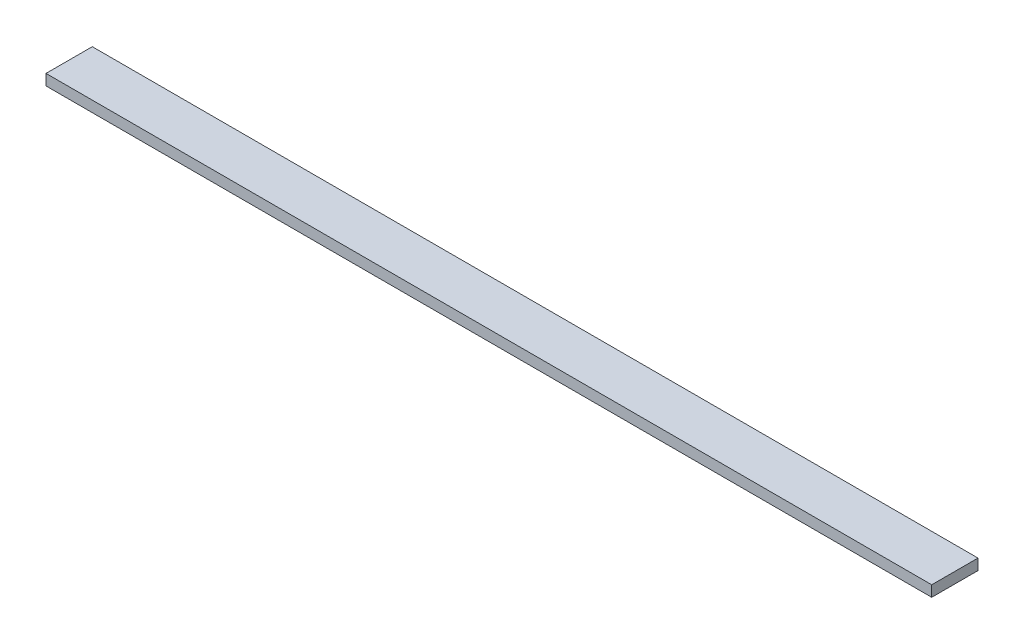
SolidWorks part; units mm, degrees
ref_plane "Front Plane" through (0, 0, 0) normal (0, 0, 1) x (1, 0, 0)
ref_plane "Top Plane" through (0, 0, 0) normal (0, 1, 0) x (1, 0, 0)
ref_plane "Right Plane" through (0, 0, 0) normal (1, 0, 0) x (0, 0, -1)
sketch "Sketch1" plane through (0, 0, 0) normal (0, 1, 0) x (1, 0, 0)
  line L1 (-486.156, -25.4) -> (486.156, -25.4)
  line L2 (-486.156, -25.4) -> (-486.156, 25.4)
  line L3 (-486.156, 25.4) -> (486.156, 25.4)
  line L4 (486.156, -25.4) -> (486.156, 25.4)
  line L5 (-486.156, -25.4) -> (486.156, 25.4) construction
  line L6 (-486.156, 25.4) -> (486.156, -25.4) construction
  point P0 (0, 0)
  dimension "D1" = 50.8
  dimension "D2" = 972.312
extrude "Boss-Extrude1" add sketch "Sketch1" along normal blind 11.938
